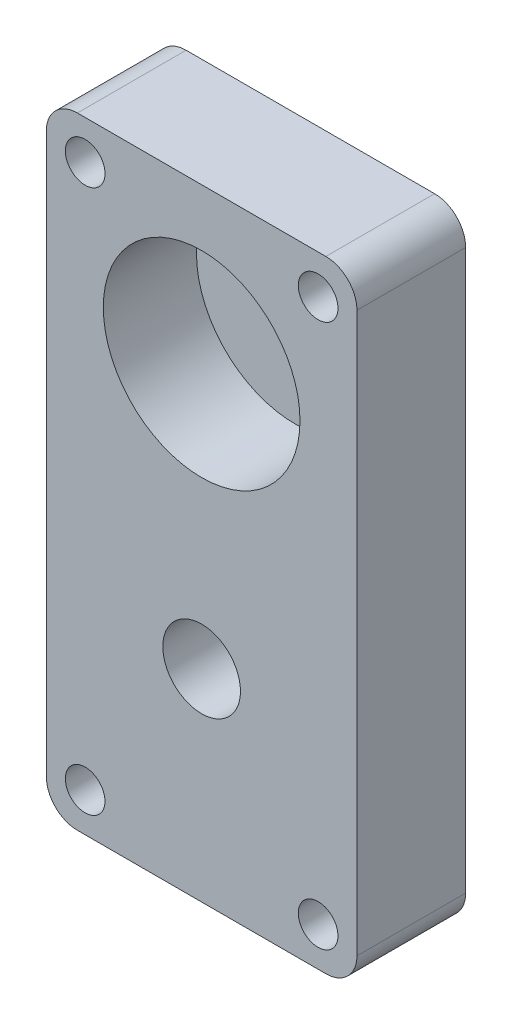
SolidWorks part; units mm, degrees
ref_plane "Front Plane" through (0, 0, 0) normal (0, 0, 1) x (1, 0, 0)
ref_plane "Top Plane" through (0, 0, 0) normal (0, 1, 0) x (1, 0, 0)
ref_plane "Right Plane" through (0, 0, 0) normal (1, 0, 0) x (0, 0, -1)
sketch "Sketch1" plane through (0, 0, 0) normal (0, 0, 1) x (1, 0, 0)
  line L2 (20, -10) -> (20, 20)
  line L3 (20, 20) -> (-20, 20)
  line L4 (-20, -10) -> (-20, 20)
  line L5 (-20, -10) -> (-20, -60)
  line L6 (20, -10) -> (20, -60)
  line L8 (-20, -60) -> (20, -60)
  line L11 (15, -20) -> (-15, -20) construction
  line L12 (-15, 15) -> (15, 15) construction
  line L13 (-15, 15) -> (-15, -55) construction
  line L14 (-15, -55) -> (15, -55) construction
  line L15 (15, 15) -> (15, -55) construction
  circle A0 centre (0, 0) radius 12.665
  circle A1 centre (-15, 15) radius 2.5546
  circle A2 centre (15, 15) radius 2.5546
  circle A5 centre (15, -15) radius 2.5546 [skipped]
  circle A6 centre (-15, -15) radius 2.5546 [skipped]
  circle A7 centre (-15, -55) radius 2.5546
  circle A8 centre (15, -55) radius 2.5546
  circle A9 centre (0, -34) radius 5
  point P0 (0, 0)
  point P19 (0, 20)
  point P25 (0, 0)
  dimension "D2" = 25.33
  dimension "D5" = 30
  dimension "D6" = 5.1092
  dimension "D9" = 10
  dimension "D1" = 40
  dimension "D3" = 80
  dimension "D4" = 20
  dimension "D7" = 4
  dimension "D8" = 70
  dimension "D10" = 34
extrude "Boss-Extrude1" add sketch "Sketch1" along normal blind 14
fillet "Fillet1" radius 4 4 edges at (-20, 20, 7) (20, 20, 7) (20, -60, 7) (-20, -60, 7)
sketch "Sketch6" plane through (0, 0, 14) normal (0, 0, 1) x (1, 0, 0)
  line L0 (-20, 16) -> (-20, -56) construction
  point P0 (-14.1999, 14.9104)
  point P1 (16, 14.9104)
  point P2 (-16, -9.8296)
  point P3 (16, -9.8299)
  dimension "D1" = 24.7403
  dimension "D2" = 30.1999
  dimension "D3" = 24.74
  dimension "D4" = 4
sketch "Sketch9" plane through (0, 0, 0) normal (0, 0, -1) x (-1, 0, 0)
  circle A0 centre (0, 0) radius 12.665 construction
  circle A1 centre (0, 0) radius 12.665
extrude "Boss-Extrude2" add sketch "Sketch9" against normal blind 2
sketch "Sketch11" plane through (0, 0, 0) normal (0, 0, -1) x (-1, 0, 0)
  circle A0 centre (0, -34) radius 7.5
extrude "Boss-Extrude3" add sketch "Sketch11" against normal blind 2
